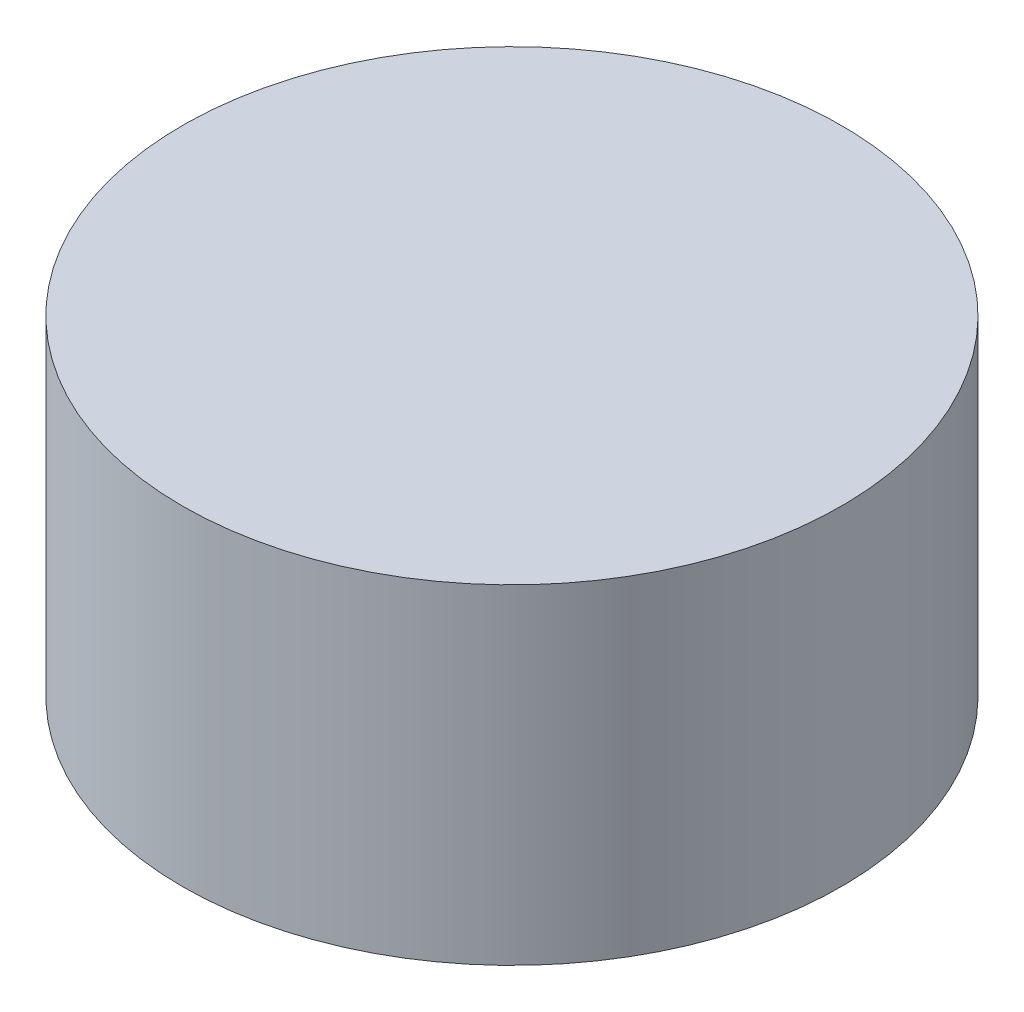
SolidWorks part; units mm, degrees
material "Настроенная пользователем пластмасса"
ref_plane "Спереди" through (0, 0, 0) normal (0, 0, 1) x (1, 0, 0)
ref_plane "Сверху" through (0, 0, 0) normal (0, 1, 0) x (1, 0, 0)
ref_plane "Справа" through (0, 0, 0) normal (1, 0, 0) x (0, 0, -1)
sketch "Эскиз1" plane through (0, 0, 0) normal (0, 0, 1) x (1, 0, 0)
  line L0 (0, 0) -> (-7, 0)
  line L1 (-7, 0) -> (-7, 7)
  line L2 (-7, 7) -> (0, 7)
  line L3 (0, 7) -> (0, 0)
revolve "Повернуть1" add sketch "Эскиз1" angle 360 about L3
